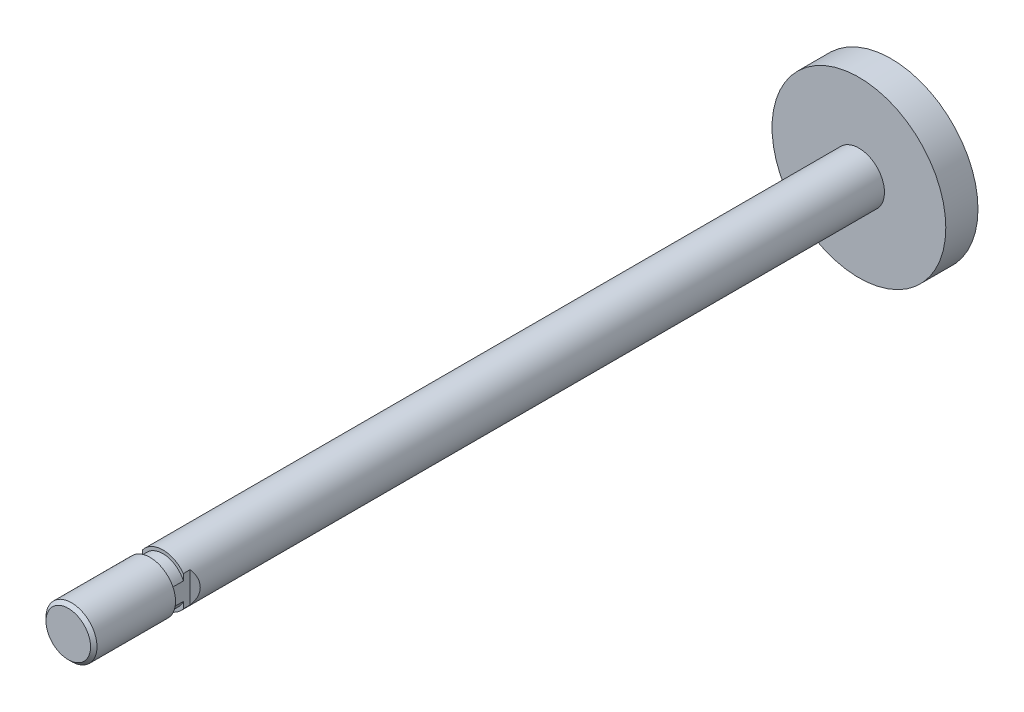
SolidWorks part; units mm, degrees
material "AISI 316 Annealed Stainless Steel Bar (SS)"
ref_plane "Front" through (0, 0, 0) normal (0, 0, 1) x (1, 0, 0)
ref_plane "Top" through (0, 0, 0) normal (0, 1, 0) x (1, 0, 0)
ref_plane "Right" through (0, 0, 0) normal (1, 0, 0) x (0, 0, -1)
sketch "Sketch1" plane through (0, 0, 0) normal (0, 0, 1) x (1, 0, 0)
  circle A0 centre (0, 0) radius 3.9624
  dimension "MM" = 7.9248
extrude "Extrude1" add sketch "Sketch1" along normal up to surface (125.2855 mm away)
sketch "Sketch2" plane through (0, 0, 0) normal (0, 0, 1) x (1, 0, 0)
  circle A0 centre (0, 0) radius 13.4938
  dimension "Bore" = 26.9875
extrude "Piston" add sketch "Sketch2" along normal mid plane 5
sketch "Sketch3" plane through (0, 0, 0) normal (1, 0, 0) x (0, 0, -1)
  line L0 (-125.2855, 13.4938) -> (-110.5855, 13.4938)
  line L1 (-125.2855, 13.4938) -> (-125.2855, 3.46)
  line L2 (-125.2855, 3.46) -> (-124.7855, 3.96)
  line L3 (-124.7855, 3.96) -> (-112.5855, 3.96)
  line L4 (-112.5855, 3.96) -> (-112.5855, 3.46)
  line L5 (-112.5855, 3.46) -> (-110.5855, 3.46)
  line L6 (-110.5855, 3.46) -> (-110.5855, 13.4938)
  line L8 (-125.2855, 3.9624) -> (-125.2855, -3.9624) construction
  line L9 (2.5, 13.4938) -> (-2.5, 13.4938) construction
  line L10 (0, 0) -> (-105.1844, 0) construction
  dimension "D1" = 45
  dimension "KK" = 7.92
  dimension "D2" = 0.5
  dimension "D3" = 2
  dimension "D4" = 0.5
  dimension "A" = 12.7
revolve "Threads" cut sketch "Sketch3" angle 360 about L10
sketch "Sketch4" plane through (0, 0, 0) normal (0, 1, 0) x (1, 0, 0)
  line L0 (0, 0) -> (0, -104.7006) construction
  line L1 (3.9624, -112.5855) -> (3.175, -112.5855)
  line L2 (3.9624, -112.5855) -> (-3.9624, -112.5855) construction
  line L3 (3.175, -112.5855) -> (3.175, -109.5375)
  line L4 (3.175, -109.5375) -> (3.9624, -108.7501)
  line L5 (3.9624, -108.7501) -> (3.9624, -112.5855)
  line L6 (3.9624, -110.5855) -> (3.9624, -2.5) construction
  line L7 (-3.9624, -108.7501) -> (-3.9624, -112.5855)
  line L8 (-3.175, -109.5375) -> (-3.9624, -108.7501)
  line L9 (-3.175, -112.5855) -> (-3.175, -109.5375)
  line L10 (-3.9624, -112.5855) -> (-3.175, -112.5855)
  dimension "D" = 6.35
  dimension "K" = 3.048
extrude "Flats" cut sketch "Sketch4" against normal through all and the other way through all
